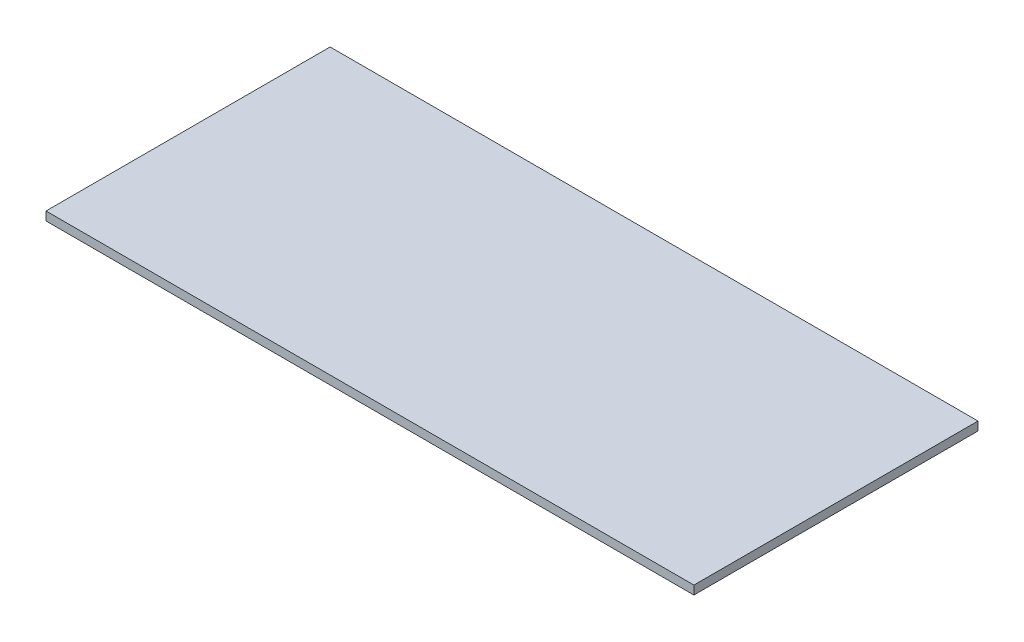
SolidWorks part; units mm, degrees
ref_plane "Front Plane" through (0, 0, 0) normal (0, 0, 1) x (1, 0, 0)
ref_plane "Top Plane" through (0, 0, 0) normal (0, 1, 0) x (1, 0, 0)
ref_plane "Right Plane" through (0, 0, 0) normal (1, 0, 0) x (0, 0, -1)
sketch "Sketch1" plane through (0, 0, 0) normal (0, 1, 0) x (1, 0, 0)
  line L1 (0, 0) -> (118.745, 0)
  line L2 (0, 0) -> (0, 52.07)
  line L3 (0, 52.07) -> (118.745, 52.07)
  line L4 (118.745, 0) -> (118.745, 52.07)
  point P7 (6.858, 47.244)
extrude "Boss-Extrude1" add sketch "Sketch1" along normal blind 1.5875
